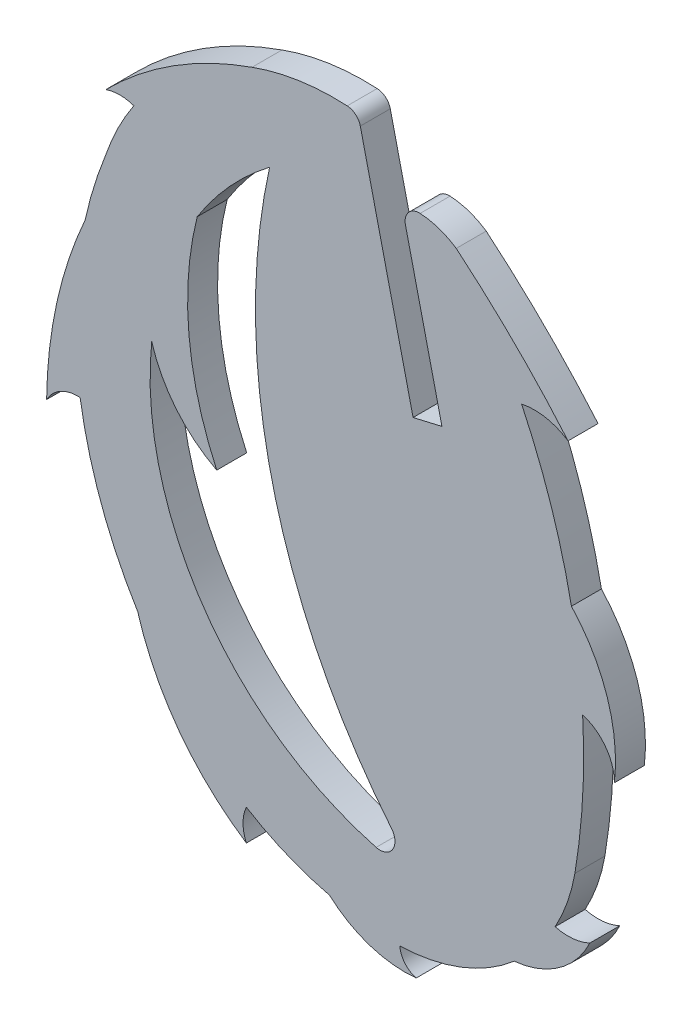
SolidWorks part; units mm, degrees
ref_plane "Front Plane" through (0, 0, 0) normal (0, 0, 1) x (1, 0, 0)
ref_plane "Top Plane" through (0, 0, 0) normal (0, 1, 0) x (1, 0, 0)
ref_plane "Right Plane" through (0, 0, 0) normal (1, 0, 0) x (0, 0, -1)
sketch "Sketch1" plane through (0, 0, 0) normal (0, 0, 1) x (1, 0, 0)
  line L0 (4.2569, 5.7694) -> (1.5728, 17.2634)
  line L1 (3.8698, 14.0509) -> (5.7237, 6.1118)
  line L2 (5.7237, 6.1118) -> (4.2569, 5.7694)
  arc A0 (12.4866, -10.1933) -> (12.8797, -3.0129) centre (-19.5383, -4.839) ccw
  arc A1 (-11.3705, 9.5299) -> (-12.4274, 6.1128) centre (8.5953, 1.483) ccw
  arc A2 (-3.0403, 13.146) -> (-6.7219, 9.1238) centre (6.3541, 0.8511) ccw
  arc A3 (-6.7219, 9.1238) -> (-5.7289, -1.5415) centre (8.8201, 5.1921) ccw
  arc A4 (3.5829, -17.8356) -> (9.4009, -15.6062) centre (3.374, -8.5845) ccw
  arc A5 (-4.2223, -15.6323) -> (0, -17.3933) centre (3.3451, -3.4299) ccw
  arc A6 (-5.7289, -1.5415) -> (-9.0343, 2.4691) centre (-2.7065, 4.317) cw
  arc A7 (0.9065, 17.8211) -> (-3.9363, 17.099) centre (0.2625, 5.5396) ccw
  arc A8 (6.4502, 14.3155) -> (4.6135, 14.9373) centre (4.4161, 11.3311) ccw
  arc A9 (-9.0343, 2.4691) -> (2.3767, -14.1023) centre (6.3541, 0.8511) ccw
  arc A10 (4.6135, 14.9373) -> (3.8698, 14.0509) centre (4.574, 14.2153) ccw
  arc A11 (1.5728, 17.2634) -> (0.9065, 17.8211) centre (0.8687, 17.099) ccw
  arc A12 (-3.0403, 13.146) -> (3.1628, -12.8839) centre (26.9484, 6.5384) ccw
  arc A13 (3.1628, -12.8839) -> (2.3767, -14.1023) centre (2.5726, -13.3659) cw
  arc A14 (-3.9363, 17.099) -> (-11.3705, 12.3988) centre (2.4962, -1.3046) ccw
  arc A15 (-11.3705, 12.3988) -> (-9.9454, 12.3988) centre (-10.658, 10.3811) cw
  arc A16 (-9.9454, 12.3988) -> (-11.3705, 9.5299) centre (0.2625, 5.5396) ccw
  arc A17 (-12.4274, 6.1128) -> (-14.381, -2.758) centre (7.8932, -3.0129) ccw
  arc A18 (-14.381, -2.758) -> (-12.6766, -1.8175) centre (-12.7956, -3.6164) cw
  arc A19 (-12.6766, -1.8175) -> (-9.7475, -9.7833) centre (8.5953, 1.483) ccw
  arc A20 (-9.7475, -9.7833) -> (-4.2223, -17.2128) centre (3.1806, -5.9382) ccw
  arc A21 (-4.2223, -17.2128) -> (-4.2223, -15.6323) centre (-2.4792, -16.4226) cw
  arc A22 (0, -17.3933) -> (4.4161, -18.8368) centre (3.8315, -13.1487) ccw
  arc A23 (4.4161, -18.8368) -> (3.5829, -17.8356) centre (4.6837, -17.7668) cw
  arc A24 (9.4009, -15.6062) -> (13.2448, -12.8839) centre (8.9192, -10.851) ccw
  arc A25 (13.2448, -12.8839) -> (11.481, -13.0459) centre (12.1388, -10.5251) cw
  arc A26 (11.481, -13.0459) -> (12.4866, -10.1933) centre (3.374, -8.5845) ccw
  arc A27 (6.4502, 14.3155) -> (12.1388, 8.6814) centre (-23.7006, -21.8163) cw
  arc A28 (12.1388, 8.6814) -> (9.7755, 9.1238) centre (10.4254, 6.0622) ccw
  arc A29 (12.3097, 1.483) -> (14.494, -5.1995) centre (6.1378, -4.2326) cw
  arc A30 (14.494, -5.1995) -> (12.8797, -3.0129) centre (12.2132, -5.1941) ccw
  arc A31 (12.3097, 1.483) -> (9.7755, 9.1238) centre (-19.5383, -4.839) ccw
  dimension "D1" = 0.762
extrude "Boss-Extrude1" add sketch "Sketch1" along normal blind 1.524
